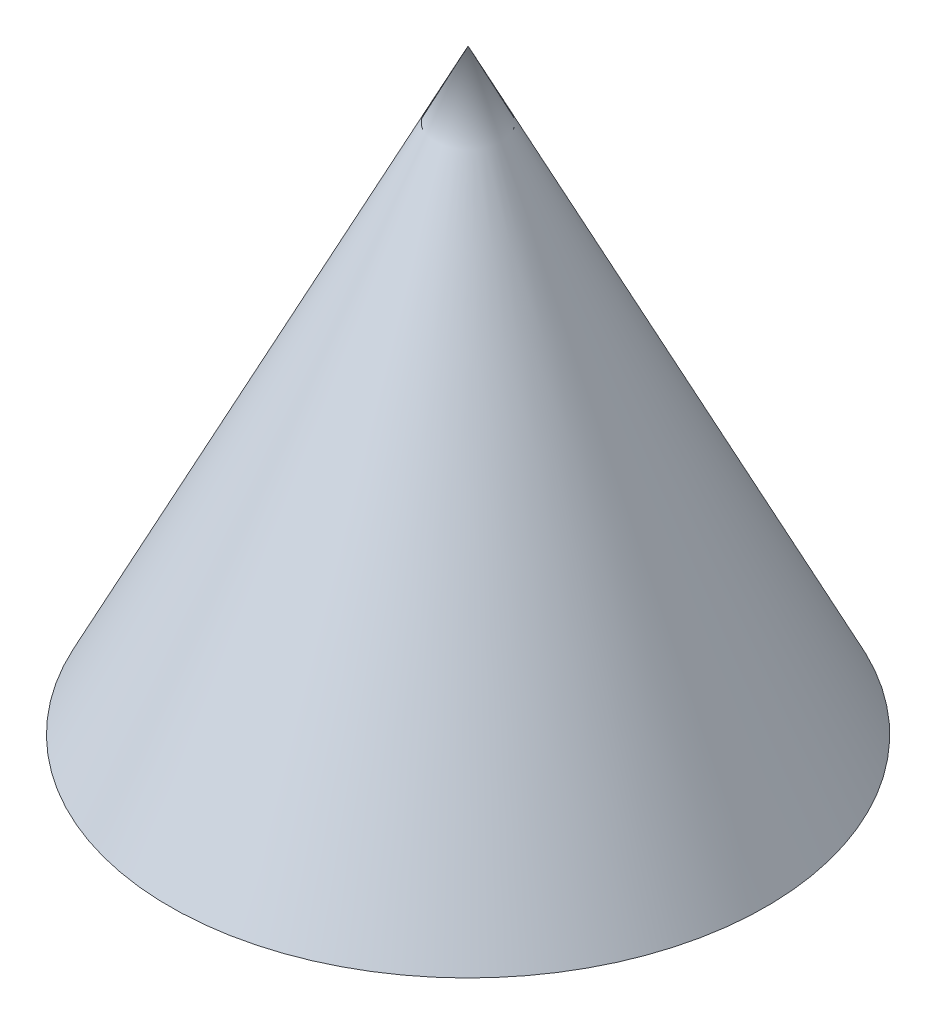
SolidWorks part; units mm, degrees
ref_plane "Front Plane" through (0, 0, 0) normal (0, 0, 1) x (1, 0, 0)
ref_plane "Top Plane" through (0, 0, 0) normal (0, 1, 0) x (1, 0, 0)
ref_plane "Right Plane" through (0, 0, 0) normal (1, 0, 0) x (0, 0, -1)
sketch "Sketch1" plane through (0, 0, 0) normal (0, 0, 1) x (1, 0, 0)
  line L0 (0, 0) -> (0, 68.4402) construction
  line L1 (0, 0) -> (25, 0)
  line L2 (0, 50) -> (25, 0)
  line L3 (0, 50) -> (0, 0)
  dimension "D1" = 25
  dimension "D2" = 50
revolve "Revolve1" add sketch "Sketch1" angle 360 about L0
